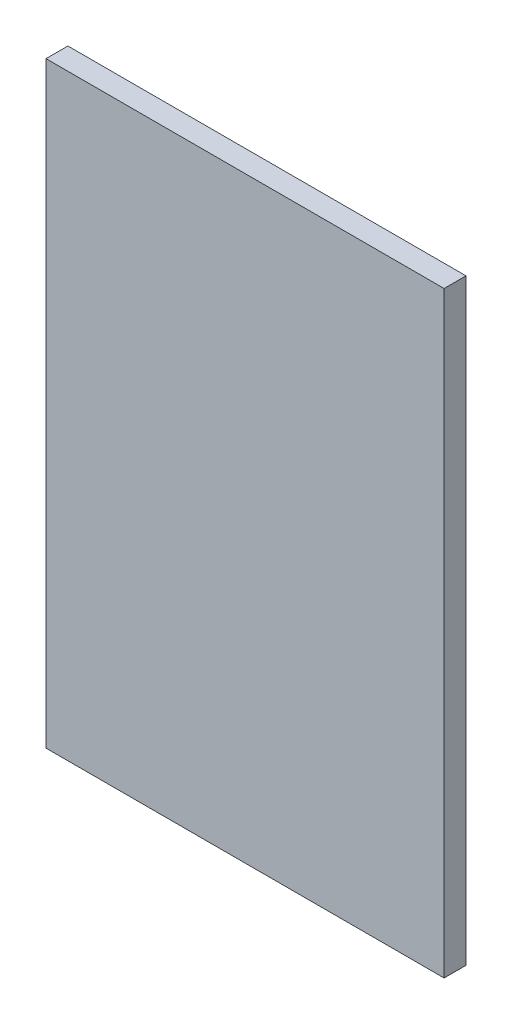
SolidWorks part; units mm, degrees
ref_plane "前视基准面" through (0, 0, 0) normal (0, 0, 1) x (1, 0, 0)
ref_plane "上视基准面" through (0, 0, 0) normal (0, 1, 0) x (1, 0, 0)
ref_plane "右视基准面" through (0, 0, 0) normal (1, 0, 0) x (0, 0, -1)
sketch "草图1" plane through (0, 0, 0) normal (0, 0, 1) x (1, 0, 0)
  line L1 (-10, -15) -> (10, -15)
  line L2 (-10, -15) -> (-10, 15)
  line L3 (-10, 15) -> (10, 15)
  line L4 (10, -15) -> (10, 15)
  line L5 (-10, -15) -> (10, 15) construction
  line L6 (-10, 15) -> (10, -15) construction
  circle A0 centre (0, 0) radius 6.25 construction
  dimension "D1" = 12.5
  dimension "D2" = 30
  dimension "D3" = 20
extrude "凸台-拉伸1" add sketch "草图1" along normal blind 1.1
